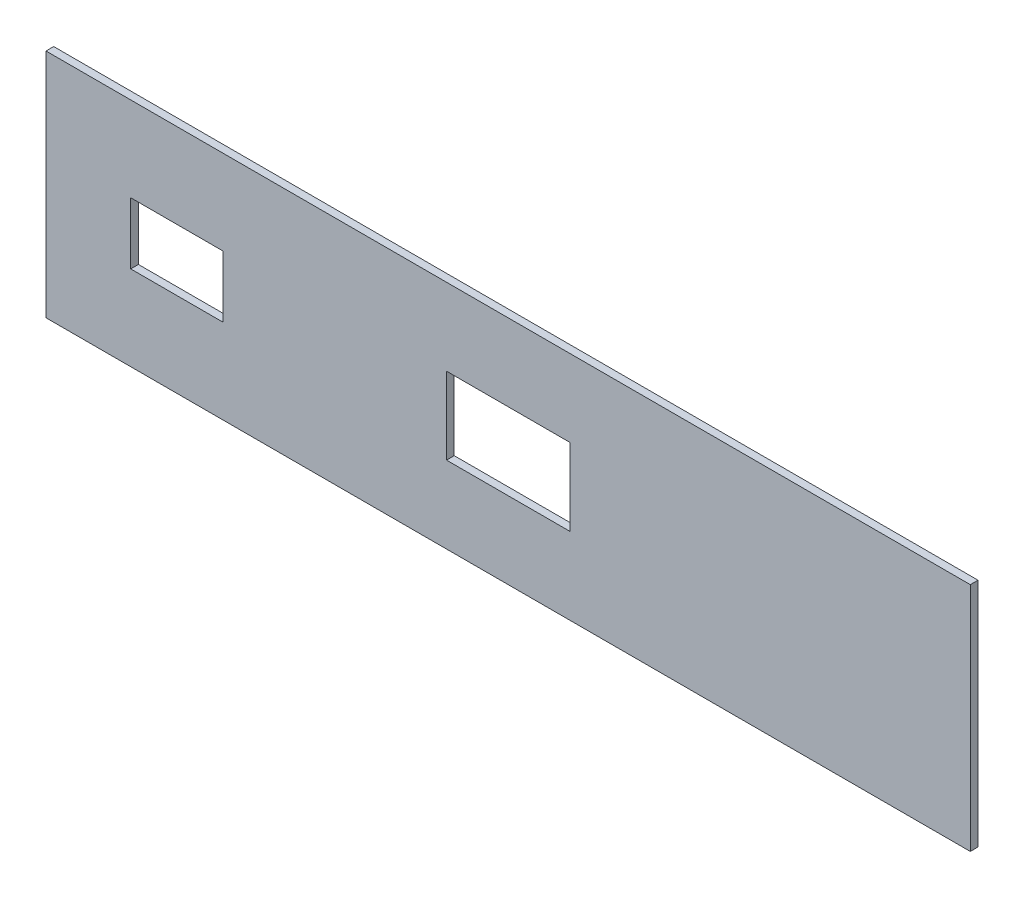
SolidWorks part; units mm, degrees
ref_plane "Front Plane" through (0, 0, 0) normal (0, 0, 1) x (1, 0, 0)
ref_plane "Top Plane" through (0, 0, 0) normal (0, 1, 0) x (1, 0, 0)
ref_plane "Right Plane" through (0, 0, 0) normal (1, 0, 0) x (0, 0, -1)
sketch "Sketch1" plane through (0, 0, 0) normal (0, 0, 1) x (1, 0, 0)
  line L0 (-130, 75) -> (-130, -75) construction
  line L1 (-300, 75) -> (300, 75)
  line L2 (-300, 75) -> (-300, -75)
  line L3 (-300, -75) -> (300, -75)
  line L4 (300, 75) -> (300, -75)
  line L5 (-300, 75) -> (300, -75) construction
  line L6 (-300, -75) -> (300, 75) construction
  line L7 (-245, 20) -> (-185, 20)
  line L8 (-245, 20) -> (-245, -20)
  line L9 (-245, -20) -> (-185, -20)
  line L10 (-185, 20) -> (-185, -20)
  line L11 (-245, 20) -> (-185, -20) construction
  line L12 (-245, -20) -> (-185, 20) construction
  line L13 (130, 75) -> (130, -75) construction
  line L14 (-40, 25) -> (40, 25)
  line L15 (-40, 25) -> (-40, -25)
  line L16 (-40, -25) -> (40, -25)
  line L17 (40, 25) -> (40, -25)
  line L18 (-40, 25) -> (40, -25) construction
  line L19 (-40, -25) -> (40, 25) construction
  point P0 (0, 0)
  point P6 (-215, 0)
  point P15 (0, 0)
  dimension "D1" = 600
  dimension "D2" = 150
  dimension "D3" = 60
  dimension "D4" = 170
  dimension "D5" = 40
  dimension "D6" = 75
  dimension "D7" = 85
  dimension "D8" = 130
  dimension "D9" = 80
  dimension "D10" = 50
  dimension "D11" = 170
extrude "Boss-Extrude1" add sketch "Sketch1" along normal blind 5
